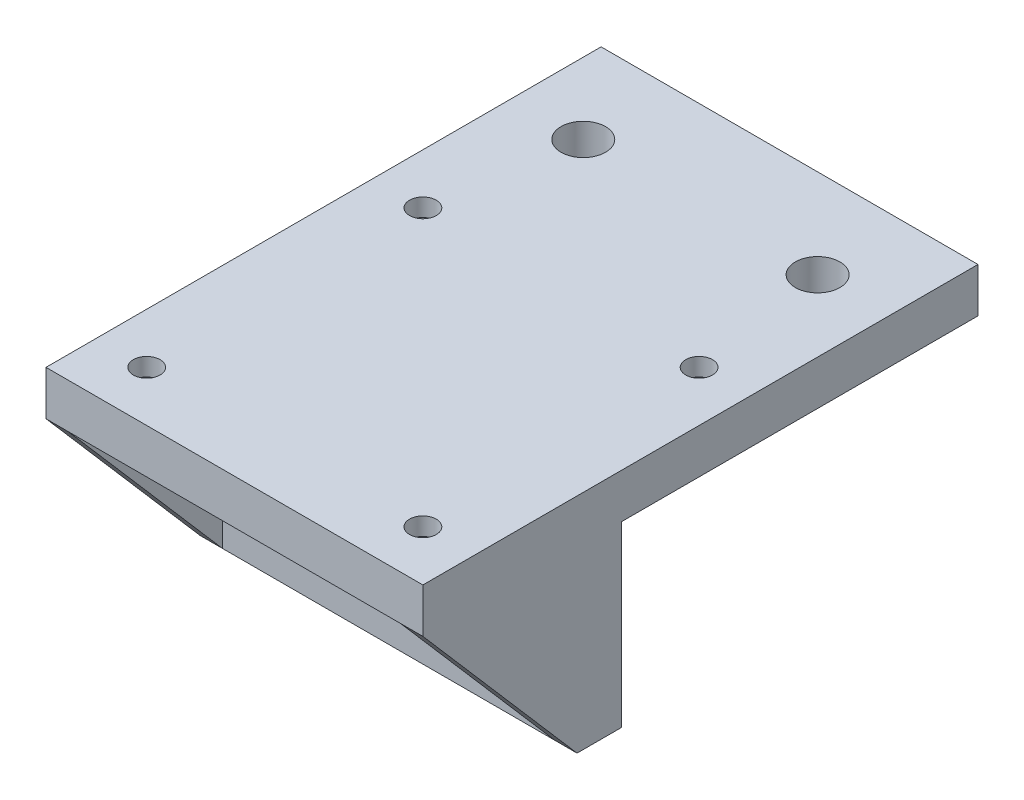
SolidWorks part; units mm, degrees
material "PET"
ref_plane "Front Plane" through (0, 0, 0) normal (0, 0, 1) x (1, 0, 0)
ref_plane "Top Plane" through (0, 0, 0) normal (0, 1, 0) x (1, 0, 0)
ref_plane "Right Plane" through (0, 0, 0) normal (1, 0, 0) x (0, 0, -1)
sketch "Sketch1" plane through (0, 0, 0) normal (0, 1, 0) x (1, 0, 0)
  line L0 (21.15, 21.15) -> (-21.15, -21.15) construction
  line L1 (-21.15, -21.15) -> (21.15, -21.15)
  line L2 (-21.15, -21.15) -> (-21.15, 21.15)
  line L4 (21.15, -21.15) -> (21.15, 21.15)
  line L5 (-15.5, 15.5) -> (15.5, -15.5) construction
  line L8 (-21.15, 21.15) -> (-21.15, 41.15)
  line L9 (-21.15, 41.15) -> (21.15, 41.15)
  line L10 (21.15, 21.15) -> (21.15, 41.15)
  circle A0 centre (-15.5, 15.5) radius 1.5
  circle A1 centre (15.5, 15.5) radius 1.5
  circle A2 centre (-15.5, -15.5) radius 1.5
  circle A3 centre (15.5, -15.5) radius 1.5
  point P4 (0, 0)
  point P15 (0, 0)
  dimension "D3" = 3
  dimension "D4" = 3
  dimension "D5" = 3
  dimension "D7" = 3
  dimension "D1" = 20
  dimension "D2" = 42.3
  dimension "D6" = 31
  dimension "D8" = 31
extrude "Boss-Extrude1" add sketch "Sketch1" along normal blind 5
sketch "Sketch2" plane through (0, 0, 0) normal (0, -1, 0) x (1, 0, 0)
  circle A0 centre (-15.5, 15.5) radius 2.75
  circle A1 centre (-15.5, -15.5) radius 2.75
  circle A2 centre (15.5, 15.5) radius 2.75
  circle A3 centre (15.5, -15.5) radius 2.75
  dimension "D1" = 5.5
  dimension "D2" = 5.5
  dimension "D3" = 5.5
  dimension "D4" = 5.5
extrude "Cut-Extrude1" cut sketch "Sketch2" against normal blind 3
sketch "Sketch3" plane through (0, 0, 0) normal (0, -1, 0) x (1, 0, 0)
  line L0 (21.15, 21.15) -> (21.15, -41.15) construction
  line L1 (-21.15, -21.15) -> (21.15, -21.15)
  line L2 (-21.15, -21.15) -> (-21.15, -1.15)
  line L3 (-21.15, -1.15) -> (21.15, -1.15)
  line L4 (21.15, -21.15) -> (21.15, -1.15)
  line L5 (21.15, -41.15) -> (-21.15, -41.15) construction
  line L6 (21.15, -1.15) -> (-21.15, -1.15)
  line L7 (21.15, -1.15) -> (21.15, 3.85)
  line L8 (21.15, 3.85) -> (-21.15, 3.85)
  line L9 (-21.15, -1.15) -> (-21.15, 3.85)
  line L10 (-21.15, -41.15) -> (-21.15, 21.15) construction
  line M8 (-21.15, 21.15) -> (-21.15, -41.15)
  line M10 (21.15, -41.15) -> (21.15, 21.15)
  dimension "D1" = 5
  dimension "D2" = 20
  dimension "D3" = 20
extrude "Boss-Extrude2" add sketch "Sketch3" along normal blind 20 contours L8 L3 M10 M8
sketch "Sketch7" plane through (0, 1.15, 3.85) normal (0, 0, -1) x (1, 0, 0)
  line L1 (-21.15, 21.15) -> (21.15, 21.15) construction
  line L2 (-21.15, 21.15) -> (-21.15, 1.15) construction
  line L3 (-21.15, 1.15) -> (21.15, 1.15) construction
  line L4 (21.15, 21.15) -> (21.15, 1.15) construction
  line L5 (-21.15, 11.15) -> (21.15, 11.15) construction
  line L6 (21.15, 21.15) -> (-21.15, 21.15) construction
  line L7 (-21.15, 21.15) -> (-21.15, 1.15) construction
  line L8 (21.15, 21.15) -> (21.15, 1.15) construction
  circle A0 centre (-13.15, 11.15) radius 2.5
  circle A1 centre (13.15, 11.15) radius 2.5
  dimension "D2" = 5
  dimension "D3" = 5
  dimension "D1" = 20
  dimension "D4" = 8
  dimension "D5" = 8
extrude "Cut-Extrude4" cut sketch "Sketch7" along normal through all
sketch "Sketch8" plane through (0, 5, 0) normal (0, 1, 0) x (1, 0, 0)
  line L0 (21.15, 41.15) -> (-21.15, 41.15) construction
  line L1 (-21.15, 41.15) -> (-21.15, -21.15) construction
  line L2 (21.15, -21.15) -> (21.15, 41.15) construction
  circle A0 centre (-13.15, 31.15) radius 2.5
  circle A1 centre (13.15, 31.15) radius 2.5
  dimension "D1" = 5
  dimension "D2" = 5
  dimension "D3" = 10
  dimension "D4" = 8
  dimension "D5" = 8
extrude "Cut-Extrude5" cut sketch "Sketch8" against normal through all
sketch "Sketch9" plane through (-21.15, 0, 0) normal (-1, 0, 0) x (0, 0, 1)
  line L0 (3.85, -20) -> (21.15, 0)
rib "Rib1" sketch "Sketch9" sketch "Sketch9" thickness 2.5 extrusion direction parallel to sketch draft on no parameters "D1"=2.5
ref_plane "Plane1" through (0, 0, 0) normal (-1, 0, 0) x (0, 0, 1)
mirror "Mirror1" about plane through (0, 0, 0) normal (-1, 0, 0) of "Rib1"
